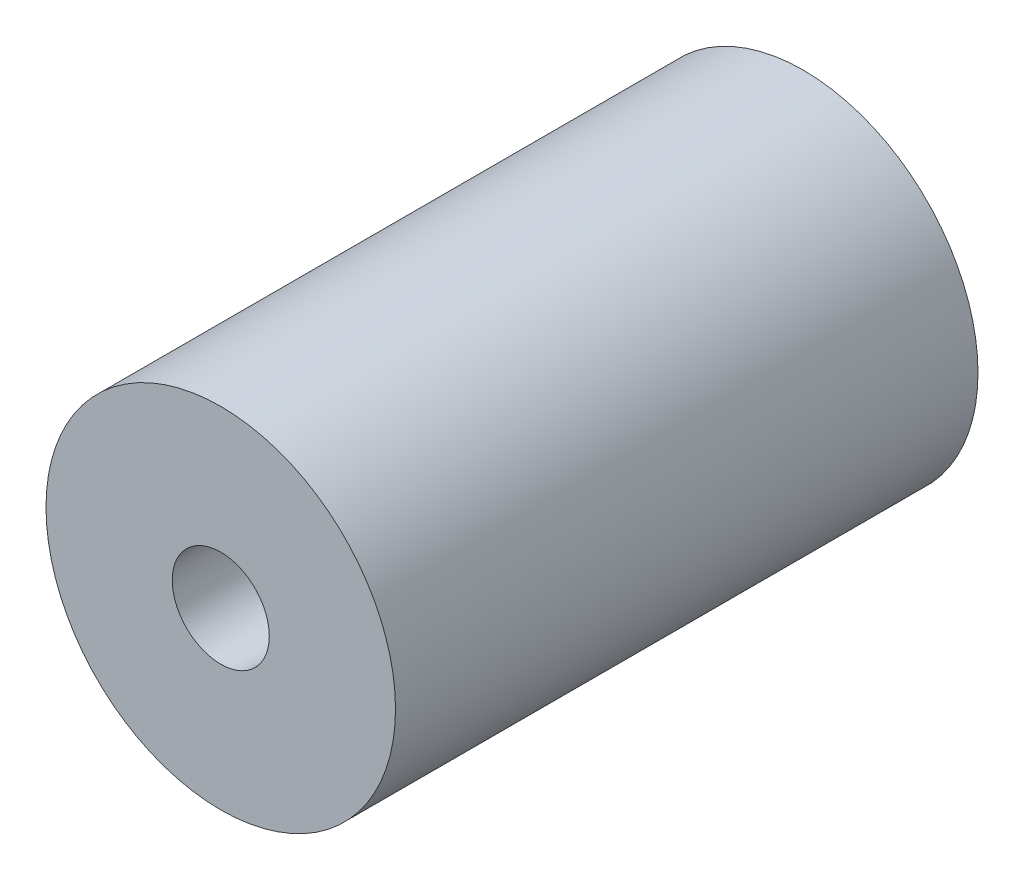
SolidWorks part; units mm, degrees
material "AISI 1020"
ref_plane "Спереди" through (0, 0, 0) normal (0, 0, 1) x (1, 0, 0)
ref_plane "Сверху" through (0, 0, 0) normal (0, 1, 0) x (1, 0, 0)
ref_plane "Справа" through (0, 0, 0) normal (1, 0, 0) x (0, 0, -1)
sketch "Эскиз1" plane through (0, 0, 0) normal (0, 0, 1) x (1, 0, 0)
  circle A0 centre (10.65, -10.65) radius 9
  circle A1 centre (10.65, -10.65) radius 8.65 construction
  dimension "D1" = 18
extrude "Бобышка-Вытянуть1" add sketch "Эскиз1" against normal blind 30
hole_wizard "Отверстие обработанное метчиком M61" positions "Эскиз2" profile "Эскиз3" tap size "M6" standard "ISO"
sketch "Эскиз2" plane through (0, 0, 0) normal (0, 0, 1) x (1, 0, 0)
  point P0 (10.65, -10.65)
sketch "Эскиз3" plane through (10.65, -10.65, 0) normal (1, 0, 0) x (0, -1, 0)
  line L0 (0, 0) -> (0, 41.5022)
  line L1 (0, 41.5022) -> (2.5, 40)
  line L2 (2.5, 40) -> (2.5, 0)
  line L5 (2.5, 0) -> (0, 0)
  line L10 (0, 41.5022) -> (-2.5, 40) construction
  line L11 (0, -6.35) -> (0, 107.95) construction
  dimension "Диаметр сверла" = 5
  dimension "Глубина сверла" = 40
  dimension "Угол заточки сверла" = 118
cosmetic thread "Отверстие резьбы1" parameters "D1"=30, "D2"=6
